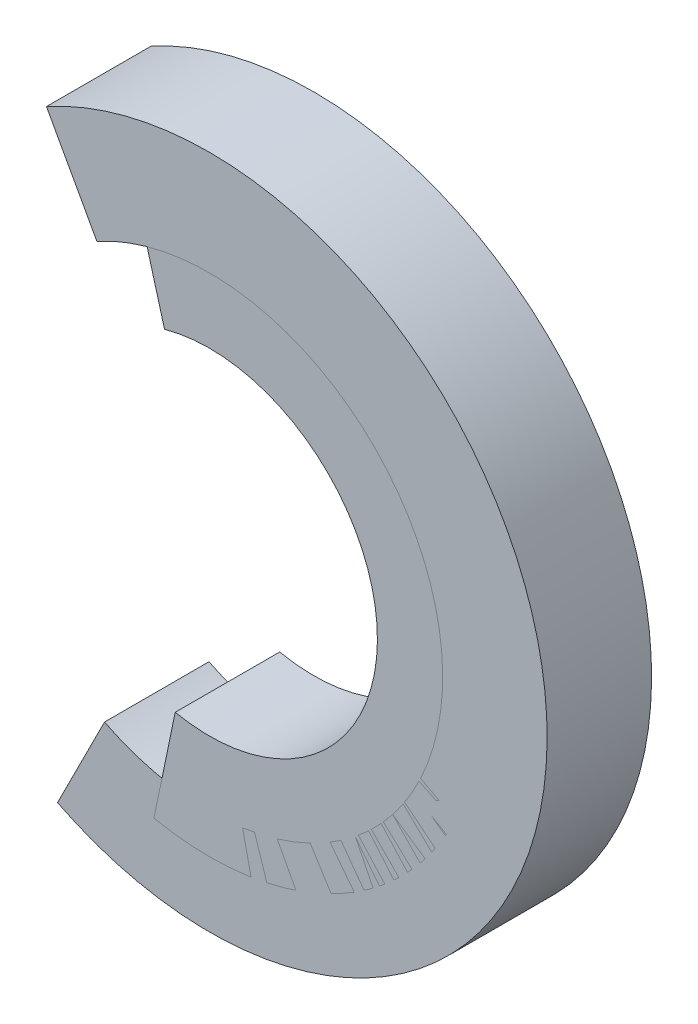
SolidWorks part; units mm, degrees
ref_plane "Front Plane" through (0, 0, 0) normal (0, 0, 1) x (1, 0, 0)
ref_plane "Top Plane" through (0, 0, 0) normal (0, 1, 0) x (1, 0, 0)
ref_plane "Right Plane" through (0, 0, 0) normal (1, 0, 0) x (0, 0, -1)
other "Graphic1"
other "Graphic (Closed) -1"
sketch "Sketch4" plane through (0, 0, 0) normal (0, 0, 1) x (1, 0, 0)
  arc A0 (56.291, -8.419) -> (57.525, -46.103) centre (61.4765, -27.1114) cw construction
  arc A5 (51.4304, -47.0487) -> (50.6997, -7.5594) centre (61.4765, -27.1114) ccw
  arc A6 (58.2008, -42.8549) -> (57.1779, -11.6159) centre (61.4765, -27.1114) ccw
  point P3 (80.8645, -26.4765)
  point P6 (0, 0)
  point P11 (0, 0)
  point P12 (54.281, -48.4046)
  point P13 (0, 0)
  point P16 (50.6805, -7.5247)
  point P17 (51.4304, -47.0487)
extrude "Extrude-Thin2" add sketch "Sketch4" along normal blind 10 thin
